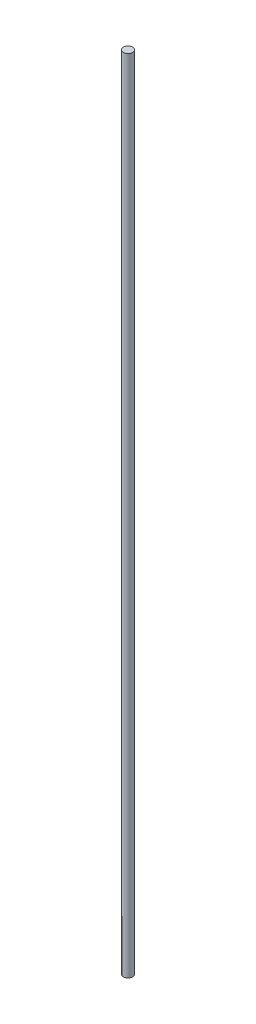
SolidWorks part; units mm, degrees
material "AISI 316 Annealed Stainless Steel Bar (SS)"
ref_plane "Front Plane" through (0, 0, 0) normal (0, 0, 1) x (1, 0, 0)
ref_plane "Top Plane" through (0, 0, 0) normal (0, 1, 0) x (1, 0, 0)
ref_plane "Right Plane" through (0, 0, 0) normal (1, 0, 0) x (0, 0, -1)
sketch "Sketch1" plane through (0, 0, 0) normal (0, 0, 1) x (1, 0, 0)
  line L0 (0, 0) -> (-3.175, 0)
  line L1 (-3.175, 0) -> (-3.175, -552.45)
  line L2 (-3.175, -552.45) -> (-1.5875, -552.45)
  line L4 (-1.5875, -542.925) -> (0, -542.925)
  line L5 (0, -542.925) -> (0, 0)
  line L6 (-1.5875, -552.45) -> (-1.5875, -542.925)
  dimension "D1" = 552.45
  dimension "D2" = 1.5875
  dimension "D3" = 9.525
  dimension "D4" = 3.175
revolve "Revolve1" add sketch "Sketch1" angle 360 about L5
